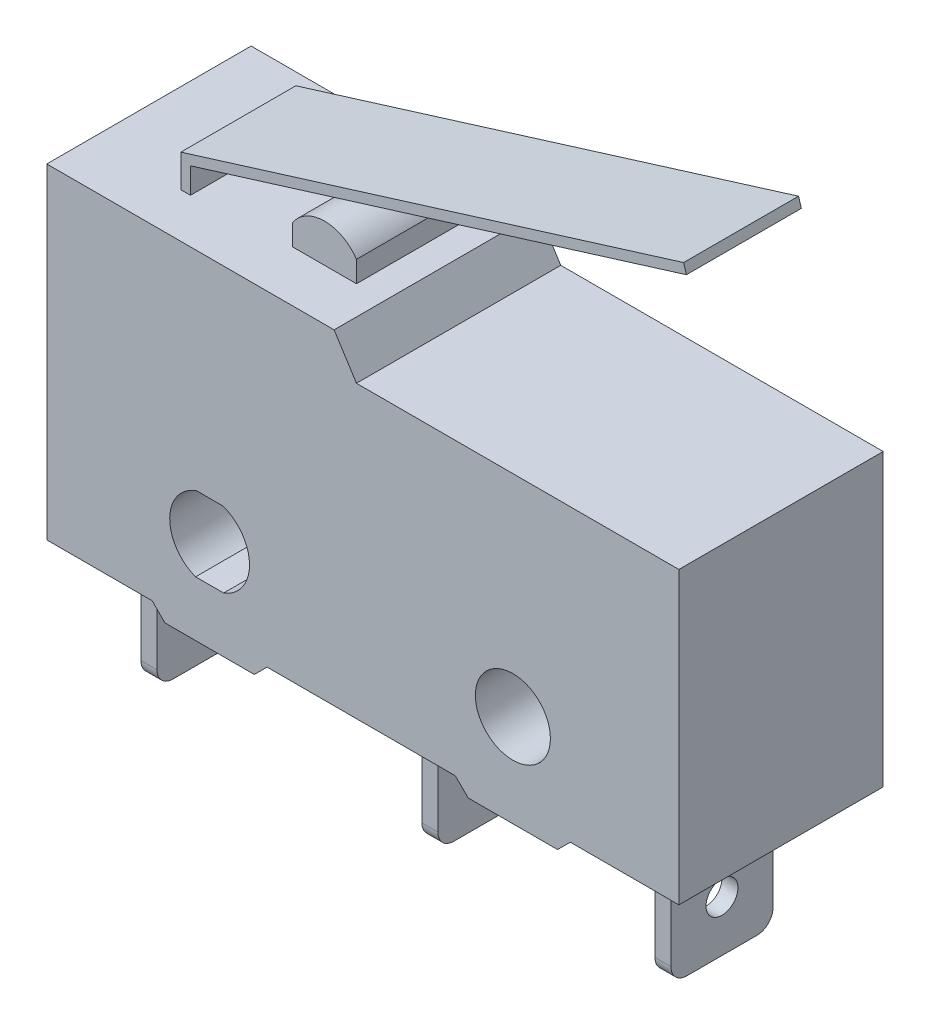
SolidWorks part; units mm, degrees
ref_plane "Plan de face" through (0, 0, 0) normal (0, 0, 1) x (1, 0, 0)
ref_plane "Plan de dessus" through (0, 0, 0) normal (0, 1, 0) x (1, 0, 0)
ref_plane "Plan de droite" through (0, 0, 0) normal (1, 0, 0) x (0, 0, -1)
ref_plane "Plan1" through (0, 0, -1.8) normal (0, 0, -1) x (-1, 0, 0)
sketch "Esquisse1" plane through (0, 0, -1.8) normal (0, 0, -1) x (-1, 0, 0)
  line L0 (7.1, 11.6211) -> (6.8888, 11.6866)
  line L1 (6.8888, 11.6866) -> (6.8, 11.4)
  line L2 (6.8, 11.4) -> (6.8, 10.6)
  line L3 (6.8, 10.6) -> (-9.9, 10.6)
  line L4 (-9.9, 10.6) -> (-9.9, 0)
  line L5 (-9.9, 0) -> (9.9, 0)
  line L6 (9.9, 0) -> (9.9, 10.6)
  line L7 (9.9, 10.6) -> (7.1, 10.6)
  line L8 (7.1, 10.6) -> (7.1, 11.6211)
  dimension "D1" = 16.7
  dimension "D2" = 16.7888
  dimension "D3" = 17
  dimension "D4" = 19.8
  dimension "D5" = 10.6
  dimension "D6" = 11.4
  dimension "D7" = 11.6211
  dimension "D8" = 11.6866
extrude "Boss.-Extru.1" add sketch "Esquisse1" against normal blind 3.6
sketch "Esquisse2" plane through (0, 0, -1.8) normal (0, 0, -1) x (-1, 0, 0)
  line L0 (9.9, 0) -> (-9.9, 0)
  line L1 (-9.9, 0) -> (-9.9, 10.6)
  line L2 (-9.9, 10.6) -> (9.9, 10.6)
  line L3 (9.9, 10.6) -> (9.9, 0)
  line L4 (7.1, 10.6) -> (7.1, 11.6211) construction
  line L5 (6.8, 10.6) -> (-9.9, 10.6) construction
  dimension "D1" = 2.8
  dimension "D2" = 17
  dimension "D3" = 10.6
extrude "Boss.-Extru.2" add sketch "Esquisse2" along normal blind 1.4
sketch "Esquisse3" plane through (0, 0, 1.8) normal (0, 0, 1) x (1, 0, 0)
  line L0 (9.9, 10.6) -> (9.9, 0)
  line L1 (9.9, 0) -> (-9.9, 0)
  line L2 (-9.9, 0) -> (-9.9, 10.6)
  line L3 (-9.9, 10.6) -> (9.9, 10.6)
  line L4 (-9.9, 0) -> (-9.9, 10.6) construction
  line L5 (9.9, 0) -> (-9.9, 0) construction
  dimension "D1" = 19.8
  dimension "D2" = 10.6
extrude "Boss.-Extru.3" add sketch "Esquisse3" along normal blind 1.4
sketch "Esquisse4" plane through (-2.982, -0.9238, 0) normal (0.9552, 0.2959, 0) x (0, 0, -1)
  line L0 (-1.8, 12.9017) -> (-1.8, 13.2017)
  line L1 (-1.8, 13.2017) -> (1.8, 13.2017)
  line L2 (1.8, 13.2017) -> (1.8, 12.9017)
  line L3 (1.8, 12.9017) -> (-1.8, 12.9017)
  line L4 (-1.8, 13.2017) -> (1.8, 13.2017) construction
  dimension "D1" = 3.6
  dimension "D2" = 0.3
extrude "Boss.-Extru.4" add sketch "Esquisse4" along normal blind 16.2656
sketch "Esquisse5" plane through (0, 0, 3.2) normal (0, 0, 1) x (1, 0, 0)
  line L0 (-0.9, 9.5) -> (9.9, 9.5)
  line L1 (9.9, 9.5) -> (9.9, 10.6)
  line L2 (9.9, 10.6) -> (-0.9, 10.6)
  line L3 (-0.9, 10.6) -> (-0.9, 9.5)
  line L4 (-9.9, 10.6) -> (-9.9, 0) construction
  line L5 (9.9, 10.6) -> (-9.9, 10.6) construction
  dimension "D1" = 9
  dimension "D2" = 19.8
  dimension "D3" = 1.1
extrude "Enlèv. mat.-Extru.1" cut sketch "Esquisse5" against normal through all
sketch "Esquisse6" plane through (0, 0, 3.2) normal (0, 0, 1) x (1, 0, 0)
  line L0 (6.1, 0.4) -> (6.1, 0)
  line L1 (6.1, 0) -> (9.9, 0)
  line L2 (9.9, 0) -> (9.9, 0.4)
  line L3 (9.9, 0.4) -> (6.1, 0.4)
  line L4 (-0.9, 10.6) -> (-0.9, 9.5) construction
  line L5 (-0.9, 9.5) -> (9.9, 9.5) construction
  dimension "D1" = 7
  dimension "D2" = 10.8
  dimension "D3" = 9.1
  dimension "D4" = 9.5
extrude "Enlèv. mat.-Extru.2" cut sketch "Esquisse6" against normal through all
sketch "Esquisse7" plane through (0, 0, 3.2) normal (0, 0, 1) x (1, 0, 0)
  line L0 (-3.4, 0) -> (3.3, 0)
  line L1 (3.3, 0) -> (3.3, 0.4)
  line L2 (3.3, 0.4) -> (-3.4, 0.4)
  line L3 (-3.4, 0.4) -> (-3.4, 0)
  line L4 (9.9, 0.4) -> (9.9, 9.5) construction
  line L5 (-0.9, 9.5) -> (9.9, 9.5) construction
  dimension "D1" = 6.6
  dimension "D2" = 13.3
  dimension "D3" = 9.1
  dimension "D4" = 9.5
extrude "Enlèv. mat.-Extru.3" cut sketch "Esquisse7" against normal through all
sketch "Esquisse8" plane through (0, 0, 3.2) normal (0, 0, 1) x (1, 0, 0)
  line L0 (-6.2, 0.4) -> (-9.9, 0.4)
  line L1 (-9.9, 0.4) -> (-9.9, 0)
  line L2 (-9.9, 0) -> (-6.2, 0)
  line L3 (-6.2, 0) -> (-6.2, 0.4)
  line L4 (6.1, 0.4) -> (6.1, 0) construction
  line L5 (3.3, 0) -> (6.1, 0) construction
  dimension "D1" = 12.3
  dimension "D2" = 16
  dimension "D3" = 0.4
extrude "Enlèv. mat.-Extru.4" cut sketch "Esquisse8" against normal through all
sketch "Esquisse9" plane through (0, 0, 3.2) normal (0, 0, 1) x (1, 0, 0)
  line L0 (-5.24, 1.73) -> (-4.36, 1.73)
  line L1 (-4.3876, 4.08) -> (-5.2124, 4.08)
  line L2 (-6.2, 0) -> (-6.2, 0.4) construction
  line L3 (3.3, 0) -> (6.1, 0) construction
  arc A0 (-5.2124, 4.08) -> (-5.24, 1.73) centre (-4.8, 2.9) ccw
  arc A1 (-4.36, 1.73) -> (-4.3876, 4.08) centre (-4.8, 2.9) ccw
  dimension "D1" = 1.25
  dimension "D2" = 1.25
  dimension "D3" = 0.96
  dimension "D4" = 0.9876
  dimension "D5" = 1.4
  dimension "D6" = 1.73
extrude "Enlèv. mat.-Extru.5" cut sketch "Esquisse9" against normal through all
ref_plane "Plan2" through (0, 0, -1.6) normal (0, 0, -1) x (-1, 0, 0)
sketch "Esquisse10" plane through (0, 0, -1.6) normal (0, 0, -1) x (-1, 0, 0)
  line L0 (1.8, 10.6) -> (3.8, 10.6)
  line L1 (3.8, 10.6) -> (3.8, 11.2633)
  line L2 (1.8, 11.2633) -> (1.8, 10.6)
  arc A0 (3.8, 11.2633) -> (1.8, 11.2633) centre (2.8, 10.6) ccw
  dimension "D1" = 1.2
  dimension "D2" = 1
extrude "Boss.-Extru.5" add sketch "Esquisse10" against normal blind 3.2
sketch "Esquisse11" plane through (0, 0.4, 0) normal (0, -1, 0) x (1, 0, 0)
  line L0 (-8.55, 1.6) -> (-8.05, 1.6)
  line L1 (-8.05, 1.6) -> (-8.05, -1.6)
  line L2 (-8.05, -1.6) -> (-8.55, -1.6)
  line L3 (-8.55, -1.6) -> (-8.55, 1.6)
  line L4 (-9.9, -3.2) -> (-9.9, 3.2) construction
  line L5 (-6.2, 3.2) -> (-9.9, 3.2) construction
  dimension "D1" = 1.35
  dimension "D2" = 1.85
  dimension "D3" = 1.6
  dimension "D4" = 4.8
extrude "Boss.-Extru.6" add sketch "Esquisse11" along normal blind 3.9
sketch "Esquisse12" plane through (0, 0.4, 0) normal (0, -1, 0) x (1, 0, 0)
  line L0 (0.25, 1.6) -> (0.75, 1.6)
  line L1 (0.75, 1.6) -> (0.75, -1.6)
  line L2 (0.75, -1.6) -> (0.25, -1.6)
  line L3 (0.25, -1.6) -> (0.25, 1.6)
  line L4 (-3.4, -3.2) -> (-3.4, 3.2) construction
  line L5 (3.3, 3.2) -> (-3.4, 3.2) construction
  dimension "D1" = 3.65
  dimension "D2" = 4.15
  dimension "D3" = 1.6
  dimension "D4" = 4.8
extrude "Boss.-Extru.7" add sketch "Esquisse12" along normal blind 3.9
sketch "Esquisse13" plane through (0, 0.4, 0) normal (0, -1, 0) x (1, 0, 0)
  line L0 (7.55, 1.6) -> (8.05, 1.6)
  line L1 (8.05, 1.6) -> (8.05, -1.6)
  line L2 (8.05, -1.6) -> (7.55, -1.6)
  line L3 (7.55, -1.6) -> (7.55, 1.6)
  line L4 (6.1, -3.2) -> (6.1, 3.2) construction
  line L5 (9.9, 3.2) -> (6.1, 3.2) construction
  dimension "D1" = 1.45
  dimension "D2" = 1.95
  dimension "D3" = 1.6
  dimension "D4" = 4.8
extrude "Boss.-Extru.8" add sketch "Esquisse13" along normal blind 3.9
draft "Dépouille1" type of draft neutral plane draft angle 32.471 faces to draft 1 face at (-0.9, 10.05, 0) neutral plane through (-9.9, 10.6, 1.8) neutral plane normal (0, 1, 0) parameters "D1"=32.471
draft "Dépouille2" type of draft neutral plane draft angle 45 faces to draft 2 face at (6.1, 0.2, 0) face at (3.3, 0.2, 0) neutral plane through (9.9, 0, 1.8) neutral plane normal (0, -1, 0) parameters "D1"=45
draft "Dépouille3" type of draft neutral plane draft angle 45 faces to draft 2 face at (-3.4, 0.2, 0) face at (-6.2, 0.2, 0) neutral plane through (9.9, 0, 1.8) neutral plane normal (0, -1, 0) parameters "D1"=45
hole_wizard "Diamètre du perçage Ø2.35 (2.35)1" positions "Esquisse15" profile "Esquisse14" hole size "Ø2.35" standard "Ansi Metric"
sketch "Esquisse15" plane through (0, 0, 3.2) normal (0, 0, 1) x (1, 0, 0)
  point P0 (4.7, 2.9)
sketch "Esquisse14" plane through (4.7, 2.9, 3.2) normal (1, 0, 0) x (0, -1, 0)
  line L0 (0, 0) -> (0, 6.4)
  line L1 (0, 6.4) -> (1.175, 6.4)
  line L2 (1.175, 6.4) -> (1.175, 0)
  line L5 (1.175, 0) -> (0, 0)
  line L11 (0, -6.35) -> (0, 107.95) construction
  dimension "Diamètre du perçage jusqu'au prochain" = 2.35
  dimension "Profondeur du perçage jusqu'au prochain" = 6.4
fillet "Congé1" radius 0.5 6 edges at (-8.3, -3.5, -1.6) (-8.3, -3.5, 1.6) (0.5, -3.5, 1.6) (0.5, -3.5, -1.6) (7.8, -3.5, -1.6) (7.8, -3.5, 1.6)
sketch "Esquisse16" plane through (-8.55, 0, 0) normal (-1, 0, 0) x (0, 0, 1)
  circle A0 centre (0, -1.9071) radius 0.5
  dimension "D1" = 1
extrude "Enlèv. mat.-Extru.6" cut sketch "Esquisse16" against normal through all
